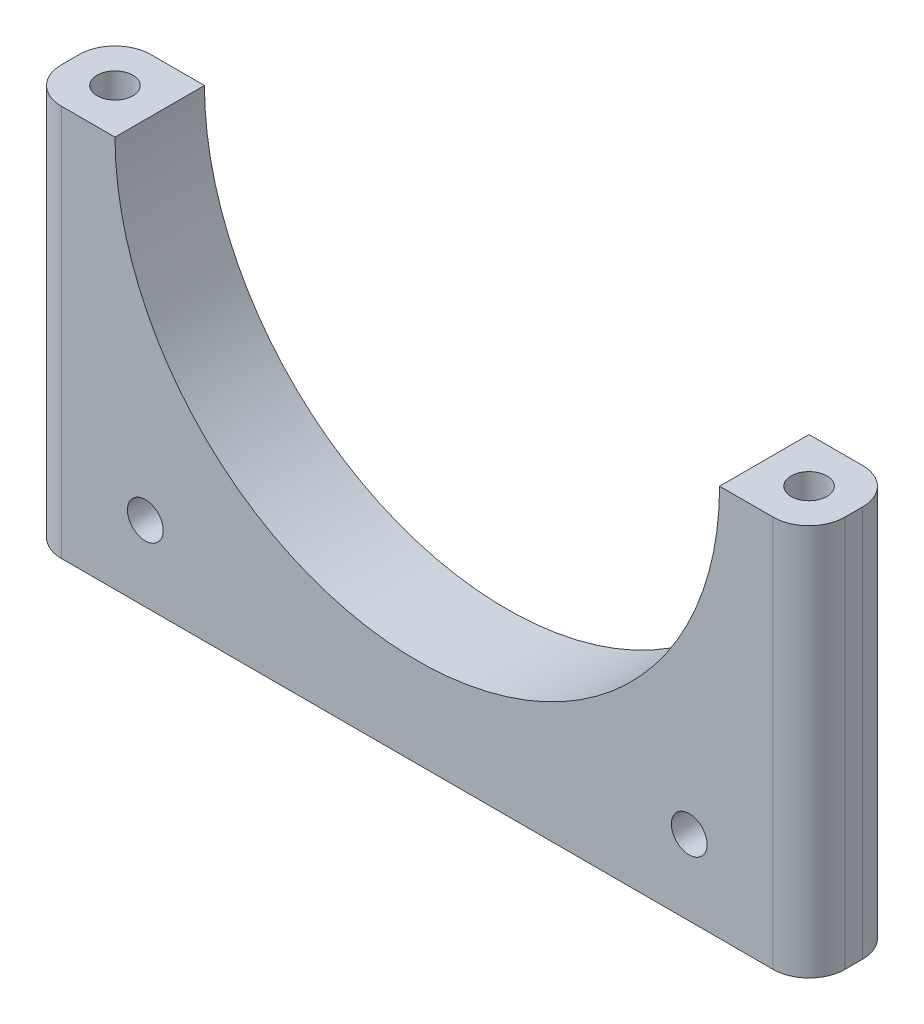
SolidWorks part; units mm, degrees
ref_plane "Front Plane" through (0, 0, 0) normal (0, 0, 1) x (1, 0, 0)
ref_plane "Top Plane" through (0, 0, 0) normal (0, 1, 0) x (1, 0, 0)
ref_plane "Right Plane" through (0, 0, 0) normal (1, 0, 0) x (0, 0, -1)
sketch "Sketch4" plane through (0, 0, 0) normal (0, 0, 1) x (1, 0, 0)
  line L0 (0, 0) -> (0, 169)
  line L1 (-84.5, 84.5) -> (84.5, 84.5)
  line L2 (0, 0) -> (0, 194)
  line L3 (-109.5, 84.5) -> (-109.5, -25)
  line L4 (109.5, 84.5) -> (109.5, -25)
  line L5 (109.5, -25) -> (0, -25)
  line L6 (0, -25) -> (-109.5, -25)
  line L7 (-109.5, 84.5) -> (109.5, 84.5)
  circle A0 centre (0, 84.5) radius 84.5
  circle A1 centre (0, 84.5) radius 109.5
  dimension "D1" = 169
  dimension "D2" = 25
extrude "Boss-Extrude1" add sketch "Sketch4" along normal blind 25 contours A1 L3 L6 | L7 A1 A0 | A1 L5 L4
sketch "Sketch5" plane through (0, 84.5, 0) normal (0, 1, 0) x (1, 0, 0)
  line L0 (0, 0) -> (0, -33.3515) construction
  line L1 (-109.5, 0) -> (-84.5, 0) construction
  line L2 (-109.5, -25) -> (-109.5, 0) construction
  circle A0 centre (-97, -12.5) radius 5
  circle A1 centre (97, -12.5) radius 5
  dimension "D1" = 10
  dimension "D2" = 12.5
  dimension "D3" = 12.5
extrude "Cut-Extrude1" cut sketch "Sketch5" against normal blind 5000 contours A0 | A1
sketch "Sketch6" plane through (0, 0, 25) normal (0, 0, 1) x (1, 0, 0)
  line L0 (-84.5, 84.5) -> (-84.5, -25)
  line L1 (109.5, -25) -> (-109.5, -25) construction
  line L3 (0, 0) -> (0, -39.0782) construction
  line L4 (0, 0) -> (0, -4) construction
  line L5 (0, -4) -> (-76.015, -4) construction
  line L6 (0, -4) -> (76.015, -4) construction
  arc A0 (-84.5, 84.5) -> (84.5, 84.5) centre (0, 84.5) ccw construction
  circle A1 centre (-76.015, -4) radius 5
  circle A2 centre (76.015, -4) radius 5
  dimension "D1" = 10
  dimension "D2" = 152.03
  dimension "D3" = 21
extrude "Cut-Extrude2" cut sketch "Sketch6" against normal blind 5000
fillet "Fillet2" radius 10 4 edges at (109.5, 29.75, 25) (109.5, 29.75, 0) (-109.5, 29.75, 25) (-109.5, 29.75, 0)
